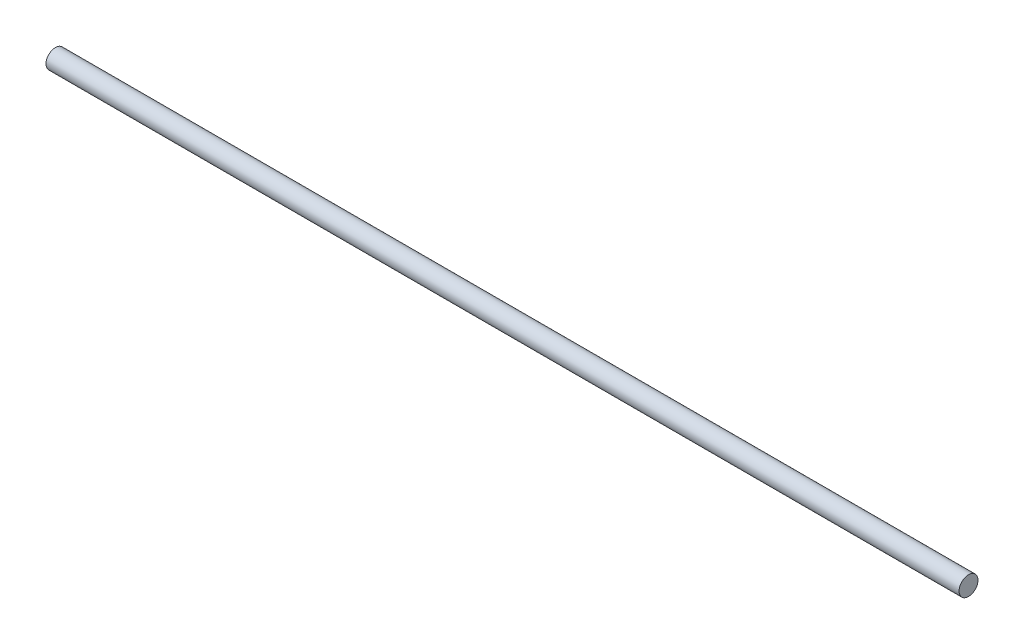
SolidWorks part; units mm, degrees
material "1060 Alloy"
ref_plane "Front Plane" through (0, 0, 0) normal (0, 0, 1) x (1, 0, 0)
ref_plane "Top Plane" through (0, 0, 0) normal (0, 1, 0) x (1, 0, 0)
ref_plane "Right Plane" through (0, 0, 0) normal (1, 0, 0) x (0, 0, -1)
sketch "Sketch1" plane through (0, 0, 0) normal (1, 0, 0) x (0, 0, -1)
  circle A0 centre (0, 0) radius 6.35
  dimension "D1" = 12.7
extrude "Boss-Extrude1" add sketch "Sketch1" along normal mid plane 612.775
